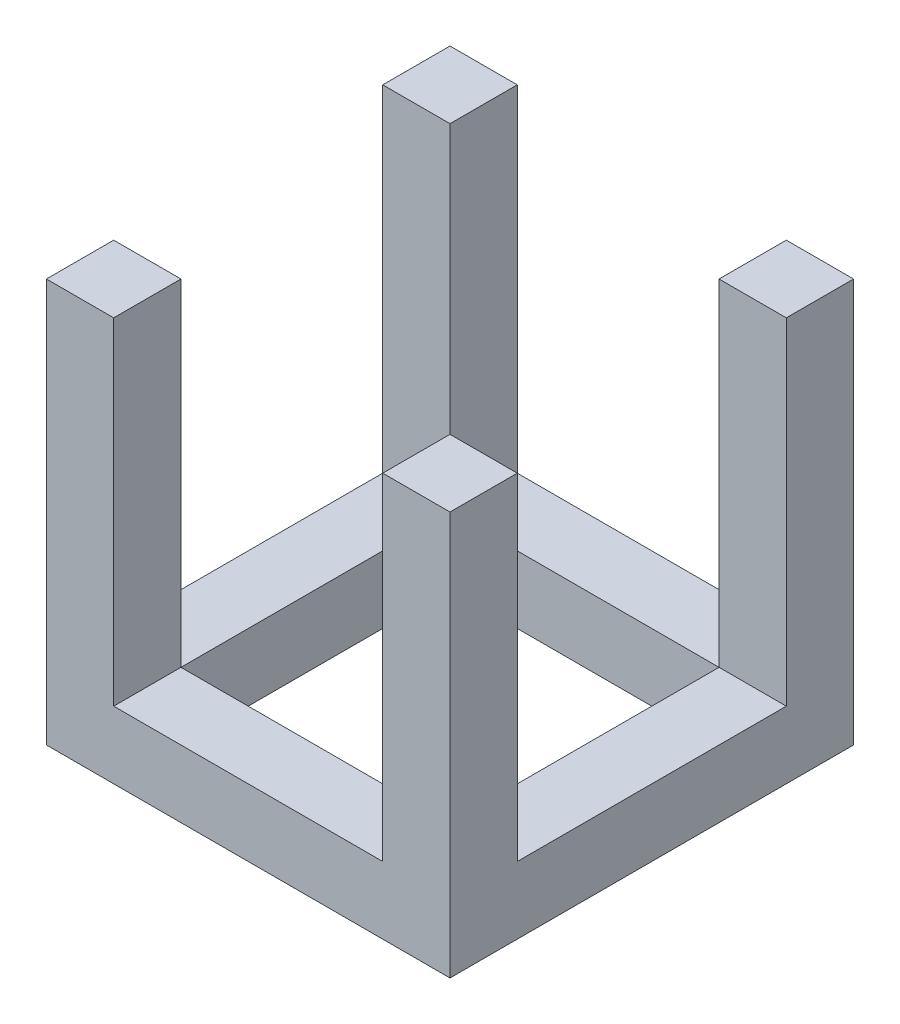
SolidWorks part; units mm, degrees
ref_plane "Plan de face" through (0, 0, 0) normal (0, 0, 1) x (1, 0, 0)
ref_plane "Plan de dessus" through (0, 0, 0) normal (0, 1, 0) x (1, 0, 0)
ref_plane "Plan de droite" through (0, 0, 0) normal (1, 0, 0) x (0, 0, -1)
sketch "Esquisse1" plane through (0, 0, 0) normal (0, 1, 0) x (1, 0, 0)
  line L1 (-15, -15) -> (15, -15)
  line L2 (-15, -15) -> (-15, 15)
  line L3 (-15, 15) -> (15, 15)
  line L4 (15, -15) -> (15, 15)
  line L5 (-15, -15) -> (15, 15) construction
  line L6 (-15, 15) -> (15, -15) construction
  line L7 (-10, -10) -> (10, -10)
  line L8 (-10, -10) -> (-10, 10)
  line L9 (-10, 10) -> (10, 10)
  line L10 (10, -10) -> (10, 10)
  line L11 (-10, -10) -> (10, 10) construction
  line L12 (-10, 10) -> (10, -10) construction
  point P0 (0, 0)
  point P6 (0, -15)
  point P7 (0, 0)
  dimension "D1" = 30
  dimension "D2" = 30
  dimension "D3" = 20
extrude "Boss.-Extru.1" add sketch "Esquisse1" along normal blind 30
sketch "Esquisse3" plane through (0, 0, 15) normal (0, 0, 1) x (1, 0, 0)
  line L0 (-10, 30) -> (-10, 5)
  line L1 (-10, 30) -> (10, 30)
  line L2 (-10, 5) -> (10, 5)
  line L3 (10, 30) -> (10, 5)
  line L4 (-15, 30) -> (15, 30) construction
  line L5 (-15, 0) -> (15, 0) construction
  line L6 (15, 30) -> (15, 0) construction
  dimension "D1" = 20
  dimension "D2" = 5
  dimension "D3" = 5
extrude "Enlèv. mat.-Extru.1" cut sketch "Esquisse3" against normal through all
sketch "Esquisse4" plane through (-15, 0, 0) normal (-1, 0, 0) x (0, 0, 1)
  line L0 (-10, 30) -> (-10, 5)
  line L1 (-10, 30) -> (10, 30)
  line L2 (-10, 5) -> (10, 5)
  line L3 (10, 30) -> (10, 5)
  line L4 (-15, 30) -> (15, 30) construction
  line L5 (15, 30) -> (15, 0) construction
  line L6 (-15, 0) -> (15, 0) construction
  dimension "D1" = 20
  dimension "D2" = 5
  dimension "D3" = 5
extrude "Enlèv. mat.-Extru.2" cut sketch "Esquisse4" against normal through all
